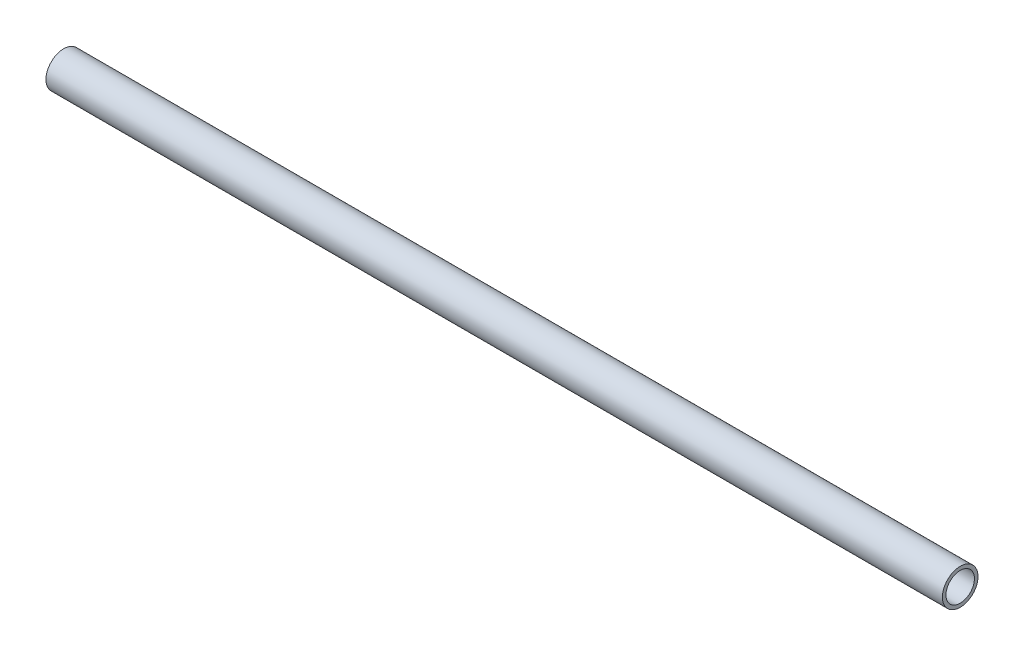
SolidWorks part; units mm, degrees
ref_plane "前基準面" through (0, 0, 0) normal (0, 0, 1) x (1, 0, 0)
ref_plane "上基準面" through (0, 0, 0) normal (0, 1, 0) x (1, 0, 0)
ref_plane "右基準面" through (0, 0, 0) normal (1, 0, 0) x (0, 0, -1)
sketch "草圖1" plane through (0, 0, 0) normal (1, 0, 0) x (0, 0, -1)
  circle A0 centre (0, 0) radius 5
  circle A1 centre (0, 0) radius 4
  dimension "D1" = 10
  dimension "D2" = 1
extrude "填料-伸長1" add sketch "草圖1" along normal mid plane 252
